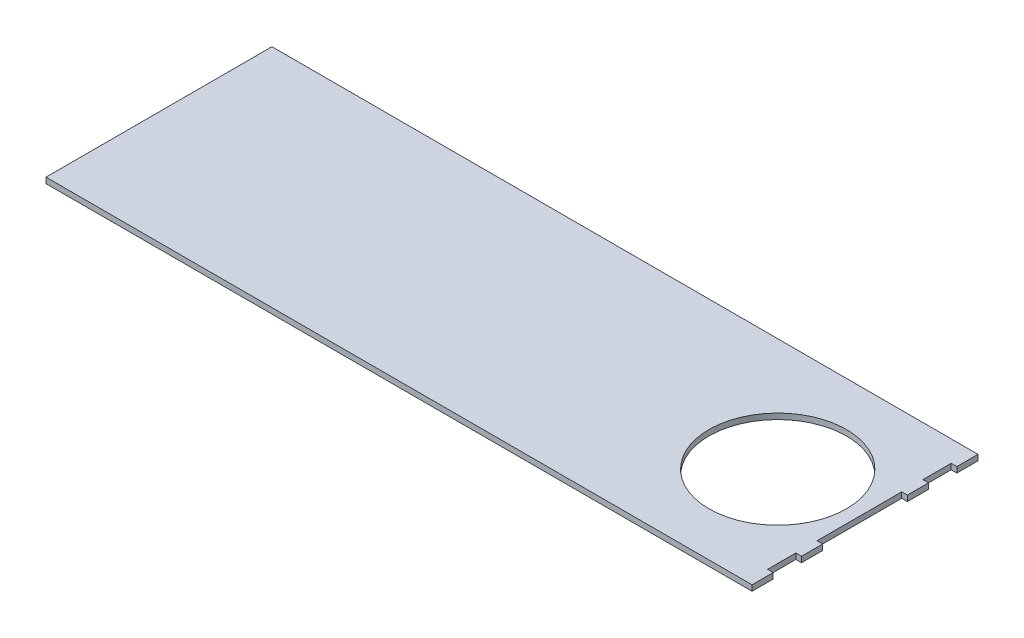
SolidWorks part; units mm, degrees
ref_plane "Front Plane" through (0, 0, 0) normal (0, 0, 1) x (1, 0, 0)
ref_plane "Top Plane" through (0, 0, 0) normal (0, 1, 0) x (1, 0, 0)
ref_plane "Right Plane" through (0, 0, 0) normal (1, 0, 0) x (0, 0, -1)
sketch "Sketch1" plane through (0, 0, 0) normal (0, 1, 0) x (1, 0, 0)
  line L1 (317.5, -101.6) -> (-317.5, -101.6)
  line L2 (317.5, -101.6) -> (317.5, 101.6)
  line L3 (317.5, 101.6) -> (-317.5, 101.6)
  line L4 (-317.5, -101.6) -> (-317.5, 101.6)
  line L5 (317.5, -101.6) -> (-317.5, 101.6) construction
  line L6 (317.5, 101.6) -> (-317.5, -101.6) construction
  point P0 (0, 0)
  dimension "D1" = 203.2
  dimension "D2" = 635
extrude "Boss-Extrude1" add sketch "Sketch1" along normal blind 5.08
sketch "Sketch2" plane through (0, 5.08, 0) normal (0, 1, 0) x (1, 0, 0)
  line L0 (317.5, -101.6) -> (317.5, 101.6) construction
  line L1 (317.5, 82.55) -> (312.42, 82.55)
  line L2 (317.5, 82.55) -> (317.5, 57.15)
  line L3 (317.5, 57.15) -> (312.42, 57.15)
  line L4 (312.42, 82.55) -> (312.42, 57.15)
  line L5 (317.5, 101.6) -> (-317.5, 101.6) construction
  line L6 (-317.5, -101.6) -> (317.5, -101.6) construction
  line L7 (317.5, -57.15) -> (312.42, -57.15)
  line L8 (317.5, -57.15) -> (317.5, -82.55)
  line L9 (317.5, -82.55) -> (312.42, -82.55)
  line L10 (312.42, -57.15) -> (312.42, -82.55)
  line L12 (317.5, 38.1) -> (312.42, 38.1)
  line L13 (317.5, 38.1) -> (317.5, -38.1)
  line L14 (317.5, -38.1) -> (312.42, -38.1)
  line L15 (312.42, 38.1) -> (312.42, -38.1)
  dimension "D1" = 5.08
  dimension "D2" = 25.4
  dimension "D3" = 19.05
  dimension "D4" = 5.08
  dimension "D5" = 19.05
  dimension "D6" = 25.4
  dimension "D7" = 5.08
  dimension "D8" = 76.2
  dimension "D9" = 19.05
  dimension "D10" = 19.05
extrude "Cut-Extrude1" cut sketch "Sketch2" against normal up to surface (5.08 mm away) up to face at (0, 0, 0)
sketch "Sketch3" plane through (0, 5.08, 0) normal (0, 1, 0) x (1, 0, 0)
  line L0 (317.5, 101.6) -> (-317.5, 101.6) construction
  line L1 (-317.5, -101.6) -> (317.5, -101.6) construction
  line L2 (312.42, 38.1) -> (312.42, -38.1) construction
  circle A0 centre (238.9665, 0) radius 61.8098
  dimension "D2" = 101.6
  dimension "D1" = 101.6
  dimension "D3" = 73.4535
extrude "Cut-Extrude2" cut sketch "Sketch3" against normal up to surface (5.08 mm away) up to face at (236.22, 0, 0)
